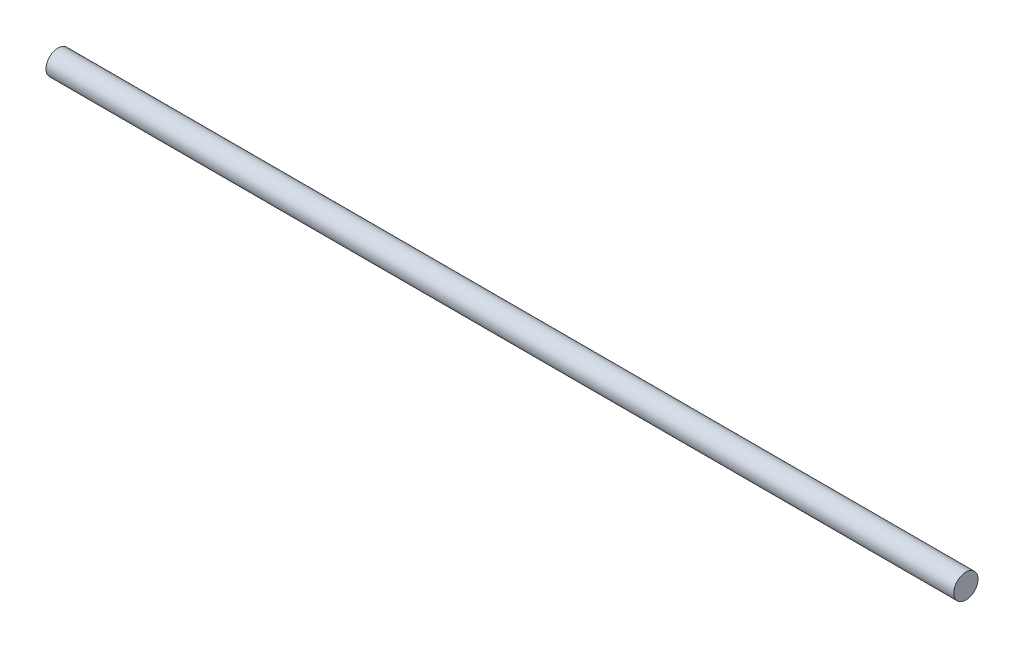
SolidWorks part; units mm, degrees
ref_plane "Front Plane" through (0, 0, 0) normal (0, 0, 1) x (1, 0, 0)
ref_plane "Top Plane" through (0, 0, 0) normal (0, 1, 0) x (1, 0, 0)
ref_plane "Right Plane" through (0, 0, 0) normal (1, 0, 0) x (0, 0, -1)
sketch "Sketch1" plane through (0, 0, 0) normal (1, 0, 0) x (0, 0, -1)
  circle A0 centre (0, 0) radius 2
  dimension "D1" = 4
extrude "Boss-Extrude1" add sketch "Sketch1" along normal blind 150
